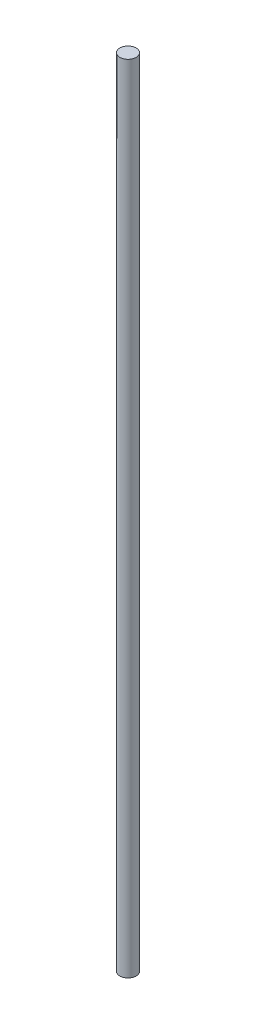
SolidWorks part; units mm, degrees
ref_plane "Front Plane" through (0, 0, 0) normal (0, 0, 1) x (1, 0, 0)
ref_plane "Top Plane" through (0, 0, 0) normal (0, 1, 0) x (1, 0, 0)
ref_plane "Right Plane" through (0, 0, 0) normal (1, 0, 0) x (0, 0, -1)
sketch "Sketch1" plane through (0, 0, 0) normal (0, 0, 1) x (1, 0, 0)
  line L0 (4, 195) -> (0, 195)
  line L1 (0, 195) -> (0, -195)
  line L2 (0, -195) -> (4, -195)
  line L3 (4, -195) -> (4, 195)
  line L4 (0, 195) -> (0, -195) construction
revolve "Revolve1" add sketch "Sketch1" angle 360 about L4
